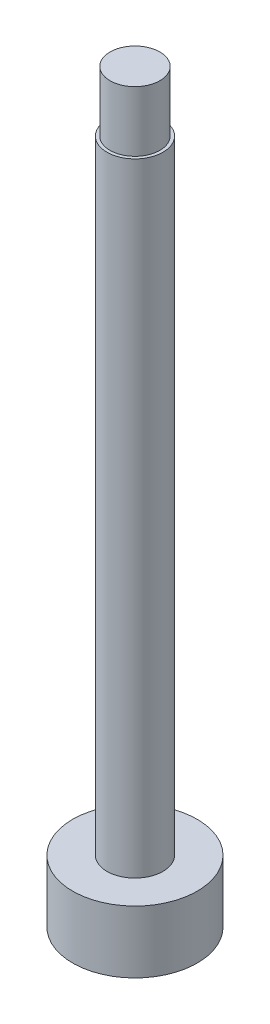
SolidWorks part; units mm, degrees
ref_plane "Front Plane" through (0, 0, 0) normal (0, 0, 1) x (1, 0, 0)
ref_plane "Top Plane" through (0, 0, 0) normal (0, 1, 0) x (1, 0, 0)
ref_plane "Right Plane" through (0, 0, 0) normal (1, 0, 0) x (0, 0, -1)
sketch "Sketch1" plane through (0, 0, 0) normal (0, 0, 1) x (1, 0, 0)
  line L0 (0, 0) -> (0, 20)
  line L1 (0, 20) -> (-0.1, 20)
  line L2 (-0.1, 20) -> (-0.1, 21.9383)
  line L3 (-0.1, 21.9383) -> (-0.9, 21.9383)
  line L4 (-0.9, 21.9383) -> (-0.9, -2)
  line L5 (-0.9, -2) -> (1.1, -2)
  line L6 (1.1, -2) -> (1.1, 0)
  line L7 (1.1, 0) -> (0, 0)
  dimension "D1" = 20
  dimension "D2" = 0.9
  dimension "D3" = 2
  dimension "D4" = 2
  dimension "D5" = 0.8
revolve "Revolve1" add sketch "Sketch1" angle 360 about L4
